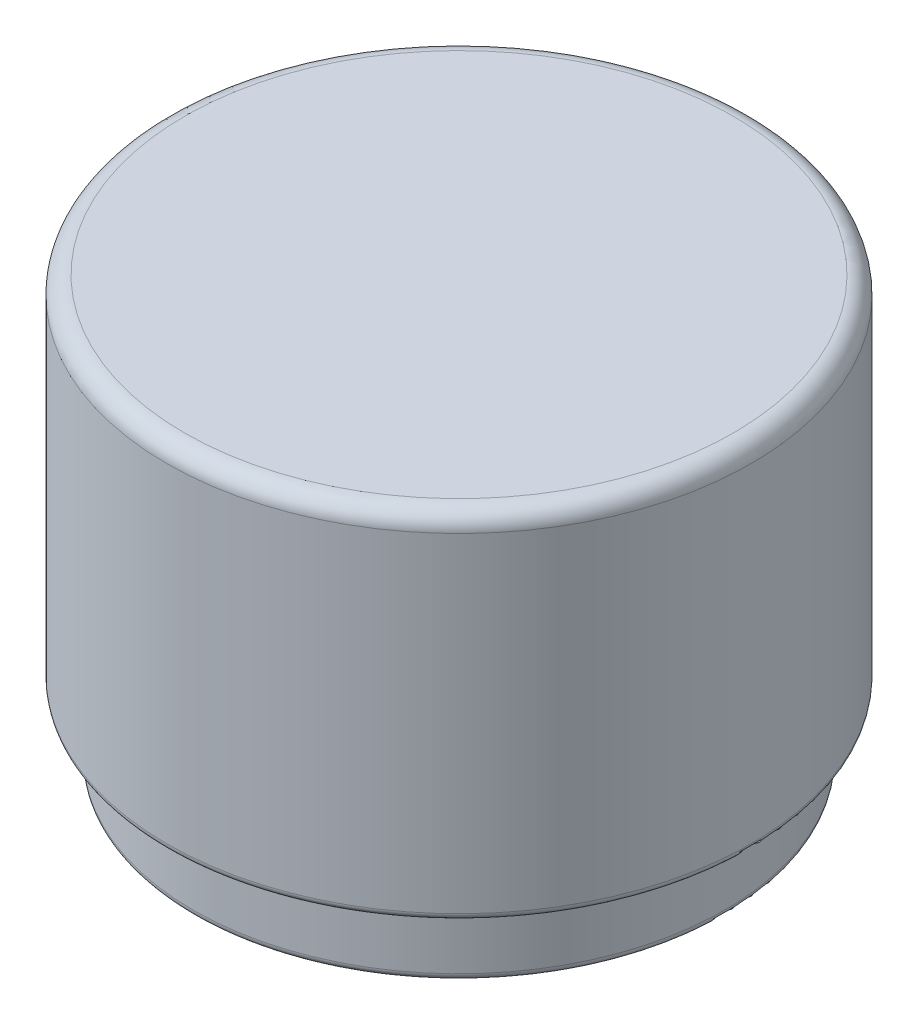
SolidWorks part; units mm, degrees
ref_plane "Front Plane" through (0, 0, 0) normal (0, 0, 1) x (1, 0, 0)
ref_plane "Top Plane" through (0, 0, 0) normal (0, 1, 0) x (1, 0, 0)
ref_plane "Right Plane" through (0, 0, 0) normal (1, 0, 0) x (0, 0, -1)
sketch "Sketch1" plane through (0, 0, 0) normal (1, 0, 0) x (0, 0, -1)
  line L0 (0, 0) -> (0, -12) construction
  line L1 (0, 0) -> (-8.25, 0)
  line L2 (0, -0.5) -> (-7.75, -0.5)
  line L3 (-7.5, -10) -> (-8.25, -10)
  line L4 (-8.25, 0) -> (-8.25, -10)
  line L5 (-7.75, -0.5) -> (-7.75, -9.5)
  line L6 (-7.5, -10) -> (-7.5, -12)
  line L7 (-7.5, -12) -> (0, -12) construction
  line L8 (-7, -9.5) -> (-7.75, -9.5)
  line L9 (-7, -9.5) -> (-7, -12)
  line L10 (0, 0) -> (0, -0.5)
  line L11 (-7, -12) -> (-7.5, -12)
  dimension "D1" = 10
  dimension "D2" = 8.25
  dimension "D3" = 12
  dimension "D4" = 7.5
  dimension "D5" = 0.5
revolve "Revolve1" add sketch "Sketch1" angle 360 about L0
fillet "Fillet1" radius 0.5 1 edges at (0, 0, 8.25)
fillet "Fillet2" radius 0.2 5 edges at (0, -0.5, 7.75) (0, -9.5, 7) (0, -12, 7) (0, -12, 7.5) (0, -10, 8.25)
